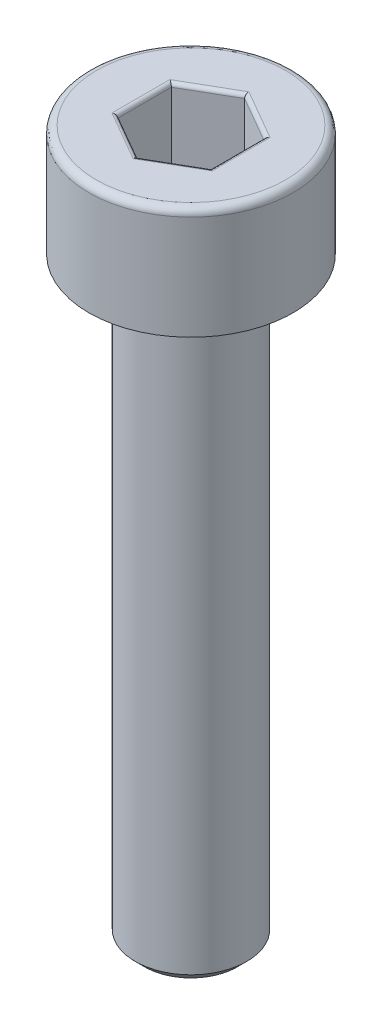
SolidWorks part; units mm, degrees
ref_plane "Front Plane" through (0, 0, 0) normal (0, 0, 1) x (1, 0, 0)
ref_plane "Top Plane" through (0, 0, 0) normal (0, 1, 0) x (1, 0, 0)
ref_plane "Right Plane" through (0, 0, 0) normal (1, 0, 0) x (0, 0, -1)
sketch "Sketch1" plane through (0, 0, 0) normal (0, 0, 1) x (1, 0, 0)
  line L0 (0, 0) -> (0, -47.0967) construction
  line L1 (0, -19) -> (-1.5, -19)
  line L2 (-1.5, -19) -> (-1.5, -3)
  line L3 (-1.5, -3) -> (-2.75, -3)
  line L4 (-2.75, -3) -> (-2.75, 0)
  line L5 (-2.75, 0) -> (0, 0)
  line L6 (0, 0) -> (0, -19)
  dimension "D1" = 16
  dimension "d" = 3
  dimension "k" = 3
  dimension "dk" = 5.5
revolve "Revolve1" add sketch "Sketch1" angle 360 about L0
chamfer "Chamfer1" distance 0.25 angle 45 2 edges at (0, -3, 1.5) (0, -19, 1.5)
fillet "Fillet1" radius 0.2 1 edges at (0, 0, 2.75)
sketch "Sketch2" plane through (0, 0, 0) normal (0, 1, 0) x (1, 0, 0)
  line L1 (0, 1.4434) -> (-1.25, 0.7217)
  line L2 (-1.25, 0.7217) -> (-1.25, -0.7217)
  line L3 (-1.25, -0.7217) -> (0, -1.4434)
  line L4 (0, -1.4434) -> (1.25, -0.7217)
  line L5 (1.25, -0.7217) -> (1.25, 0.7217)
  line L6 (1.25, 0.7217) -> (0, 1.4434)
  circle A0 centre (0, 0) radius 1.25 construction
  dimension "s" = 2.5
extrude "Cut-Extrude1" cut sketch "Sketch2" against normal blind 2
fillet "Fillet2" radius 0.1 12 edges at (-0.625, 0, -1.0825) (-1.25, 0, 0) (-0.625, 0, 1.0825) (0.625, 0, 1.0825) (1.25, 0, 0) (0.625, 0, -1.0825) (1.25, -2, 0) (0.625, -2, 1.0825) (-0.625, -2, 1.0825) (-1.25, -2, 0) (-0.625, -2, -1.0825) (0.625, -2, -1.0825)
